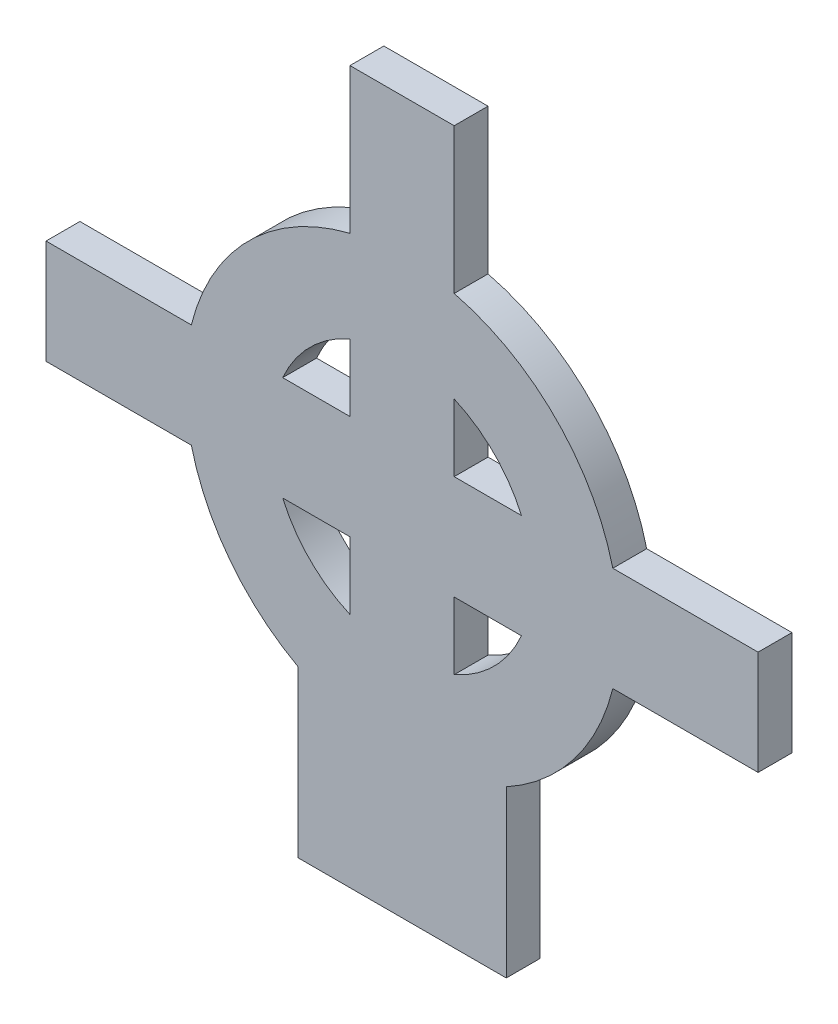
SolidWorks part; units mm, degrees
ref_plane "Alzado" through (0, 0, 0) normal (0, 0, 1) x (1, 0, 0)
ref_plane "Planta" through (0, 0, 0) normal (0, 1, 0) x (1, 0, 0)
ref_plane "Vista lateral" through (0, 0, 0) normal (1, 0, 0) x (0, 0, -1)
sketch "Croquis1" plane through (0, 0, 0) normal (0, 0, 1) x (1, 0, 0)
  line L0 (-6, 13) -> (-6, 20.5) construction
  line L1 (0, 0) -> (-12, 0)
  line L2 (0, 0) -> (0, 9.5341)
  line L4 (-12, 0) -> (-12, 9.5341)
  line L5 (14.5, 17.5) -> (6.1347, 17.5)
  line L6 (-26.5, 17.5) -> (-26.5, 23.5)
  line L7 (-26.5, 20.5) -> (-6, 20.5) construction
  line L8 (14.5, 23.5) -> (6.1347, 23.5)
  line L9 (14.5, 17.5) -> (14.5, 23.5)
  line L10 (-9, 23.5) -> (-9, 27.3739)
  line L11 (-9, 41) -> (-3, 41)
  line L12 (-3, 23.5) -> (-3, 27.3739)
  line L13 (-9, 17.5) -> (-9, 13.6261)
  line L14 (-3, 17.5) -> (-3, 13.6261)
  line L15 (-9, 17.5) -> (-12.8739, 17.5)
  line L16 (-9, 23.5) -> (-12.8739, 23.5)
  line L17 (-18.1347, 17.5) -> (-26.5, 17.5)
  line L18 (-18.1347, 23.5) -> (-26.5, 23.5)
  line L19 (-9, 32.6347) -> (-9, 41)
  line L20 (-3, 32.6347) -> (-3, 41)
  line L21 (0.8739, 17.5) -> (-3, 17.5)
  line L22 (0.8739, 23.5) -> (-3, 23.5)
  arc A0 (-9, 32.6347) -> (-18.1347, 23.5) centre (-6, 20.5) ccw
  arc A1 (-9, 27.3739) -> (-12.8739, 23.5) centre (-6, 20.5) ccw
  arc A2 (-18.1347, 17.5) -> (-12, 9.5341) centre (-6, 20.5) ccw
  arc A3 (-12.8739, 17.5) -> (-9, 13.6261) centre (-6, 20.5) ccw
  arc A4 (-3, 13.6261) -> (0.8739, 17.5) centre (-6, 20.5) ccw
  arc A5 (0.8739, 23.5) -> (-3, 27.3739) centre (-6, 20.5) ccw
  arc A6 (0, 9.5341) -> (6.1347, 17.5) centre (-6, 20.5) ccw
  arc A7 (6.1347, 23.5) -> (-3, 32.6347) centre (-6, 20.5) ccw
  point P15 (-6, 17.5)
  point P16 (-6, 23.5)
  point P22 (-6, 41)
  dimension "D3" = 25
  dimension "D4" = 5
  dimension "D5" = 3
  dimension "D6" = 20.5
  dimension "D7" = 3
extrude "Saliente-Extruir1" add sketch "Croquis1" along normal blind 1.95
sketch "Croquis2" plane through (0, 0, 4) normal (0, 0, 1) x (1, 0, 0)
  line L0 (-12, 0) -> (0, 0) construction
  line L1 (-10.6, 0) -> (-1.4, 0)
  line L2 (-10.6, 0) -> (-10.6, 12)
  line L3 (-10.6, 12) -> (-1.4, 12)
  line L4 (-1.4, 0) -> (-1.4, 12)
  point P6 (-6, 0)
  point P7 (-6, 0)
  dimension "D1" = 9.2
  dimension "D2" = 12
extrude "Cortar-Extruir1" cut sketch "Croquis2" against normal blind 2
